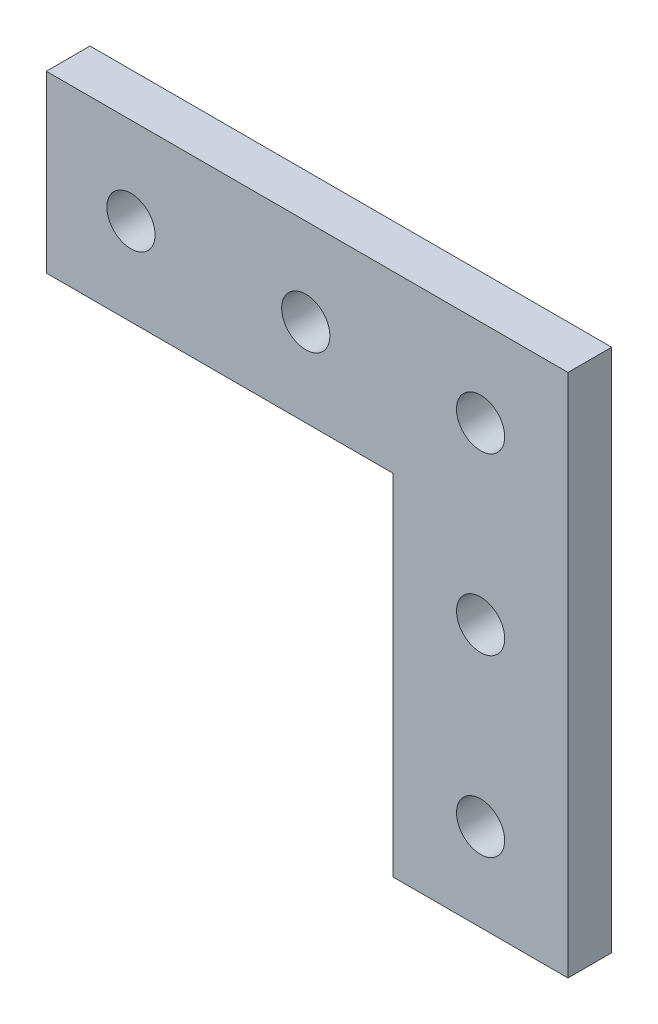
SolidWorks part; units mm, degrees
ref_plane "Front Plane" through (0, 0, 0) normal (0, 0, 1) x (1, 0, 0)
ref_plane "Top Plane" through (0, 0, 0) normal (0, 1, 0) x (1, 0, 0)
ref_plane "Right Plane" through (0, 0, 0) normal (1, 0, 0) x (0, 0, -1)
sketch "Sketch1" plane through (0, 0, 0) normal (0, 0, 1) x (1, 0, 0)
  line L0 (12.7, 0) -> (-12.7, 0)
  line L1 (-12.7, 0) -> (-12.7, 50.8)
  line L7 (12.7, 50.8) -> (12.7, 0)
  line L8 (12.7, 50.8) -> (12.7, 76.2)
  line L10 (-63.1, 76.2) -> (-63.1, 50.8)
  line L12 (12.7, 76.2) -> (-63.1, 76.2)
  line L13 (-63.1, 50.8) -> (-12.7, 50.8)
  dimension "D1" = 25.4
  dimension "D2" = 12.7
  dimension "D3" = 50.8
  dimension "D4" = 50.4
  dimension "D5" = 25.4
extrude "Boss-Extrude1" add sketch "Sketch1" along normal blind 6.35
sketch "Sketch2" plane through (0, 0, 6.35) normal (0, 0, 1) x (1, 0, 0)
  line L0 (0, 0) -> (0, 67) construction
  line L2 (-28.9, 63.5) -> (-21.9, 63.5) construction
  line L5 (-12.7, 0) -> (12.7, 0) construction
  line L6 (-3.5, 63.5) -> (3.5, 63.5) construction
  line L7 (0, 63.5) -> (-63.1, 63.5) construction
  line L8 (-63.1, 76.2) -> (-63.1, 50.8) construction
  circle A0 centre (0, 63.5) radius 3.5
  circle A2 centre (-25.4, 63.5) radius 3.5
  circle A3 centre (0, 38.1) radius 3.5
  circle A4 centre (0, 12.7) radius 3.5
  circle A5 centre (-50.8, 63.5) radius 3.5
  dimension "D1" = 7
  dimension "D2" = 7
  dimension "D3" = 7
  dimension "D4" = 7
  dimension "D5" = 7
  dimension "D6" = 12.7
  dimension "D7" = 25.4
  dimension "D8" = 25.4
  dimension "D9" = 25.4
extrude "Cut-Extrude1" cut sketch "Sketch2" against normal through all
